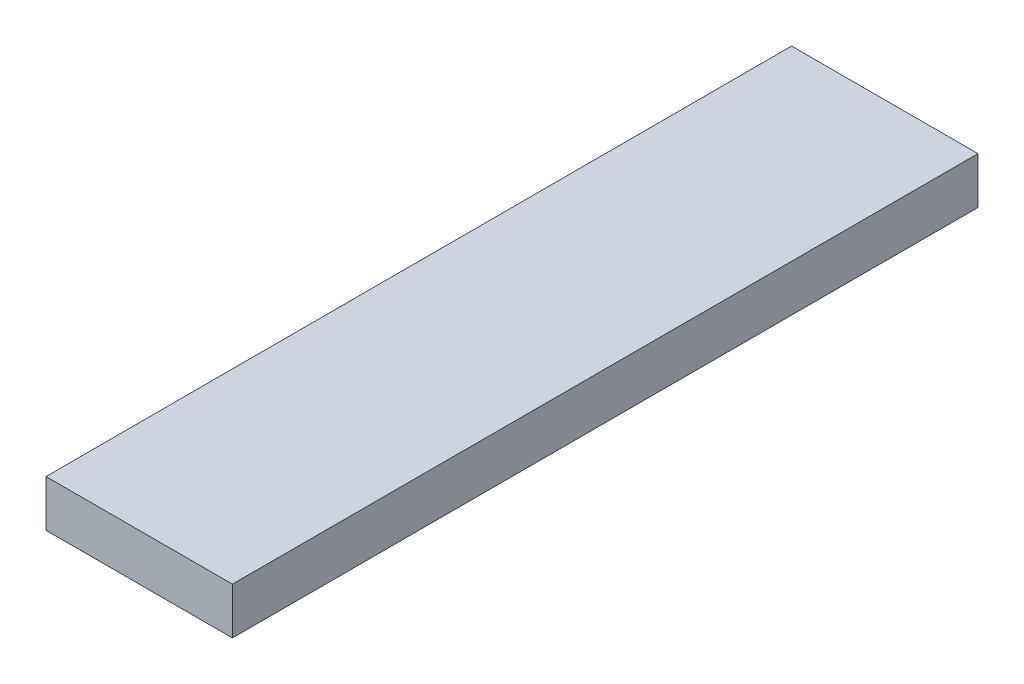
SolidWorks part; units mm, degrees
ref_plane "Plan de face" through (0, 0, 0) normal (0, 0, 1) x (1, 0, 0)
ref_plane "Plan de dessus" through (0, 0, 0) normal (0, 1, 0) x (1, 0, 0)
ref_plane "Plan de droite" through (0, 0, 0) normal (1, 0, 0) x (0, 0, -1)
sketch "Esquisse1" plane through (0, 0, 0) normal (0, 0, 1) x (1, 0, 0)
  line L0 (-4, 0) -> (4, 0)
  line L1 (4, 0) -> (4, -2)
  line L2 (4, -2) -> (2.5, -3.5)
  line L3 (2.5, -3.5) -> (-2.5, -3.5)
  line L4 (-2.5, -3.5) -> (-4, -2)
  line L5 (-4, -2) -> (-4, 0)
  line L6 (-4, -2) -> (4, -2) construction
  line L7 (0, 0) -> (0, -3.5) construction
  point P8 (0, 0)
  dimension "D1" = 2
  dimension "D2" = 8
  dimension "D3" = 1.5
extrude "Boss.-Extru.1" add sketch "Esquisse1" along normal blind 32
chamfer "Chanfrein1" distance 1.5 angle 45 2 edges at (0, -3.5, 0) (0, -3.5, 32)
